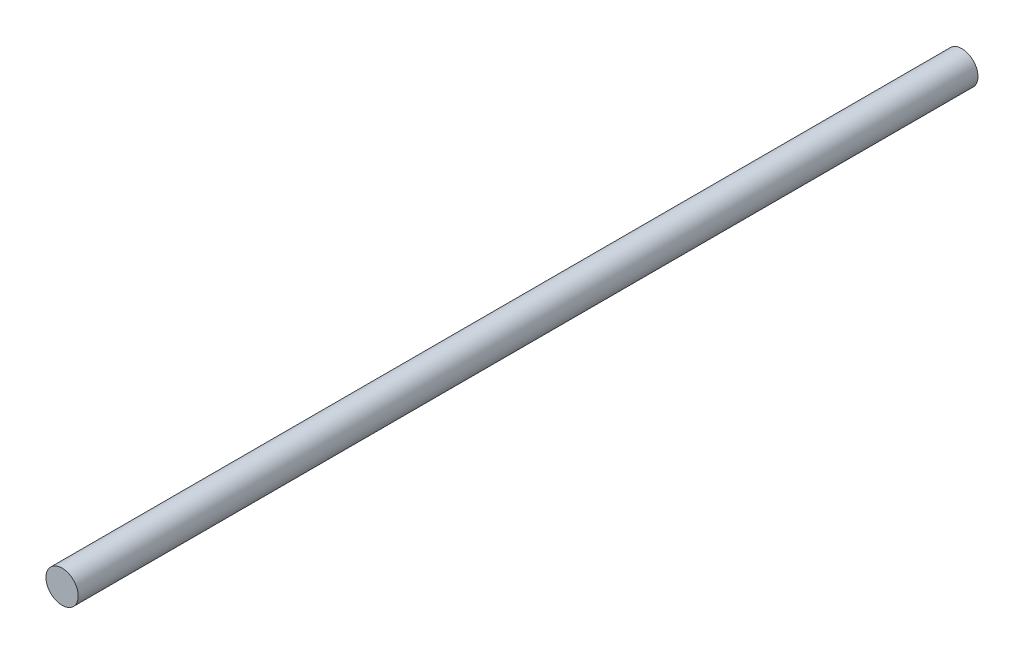
SolidWorks part; units mm, degrees
ref_plane "Front Plane" through (0, 0, 0) normal (0, 0, 1) x (1, 0, 0)
ref_plane "Top Plane" through (0, 0, 0) normal (0, 1, 0) x (1, 0, 0)
ref_plane "Right Plane" through (0, 0, 0) normal (1, 0, 0) x (0, 0, -1)
sketch "Sketch1" plane through (0, 0, 0) normal (0, 0, 1) x (1, 0, 0)
  circle A0 centre (0, 0) radius 4
  dimension "D1" = 8
extrude "Boss-Extrude1" add sketch "Sketch1" along normal blind 223.3
move or copy body "Body-Move/Copy1" [suppressed] bodies to move or copy 101
